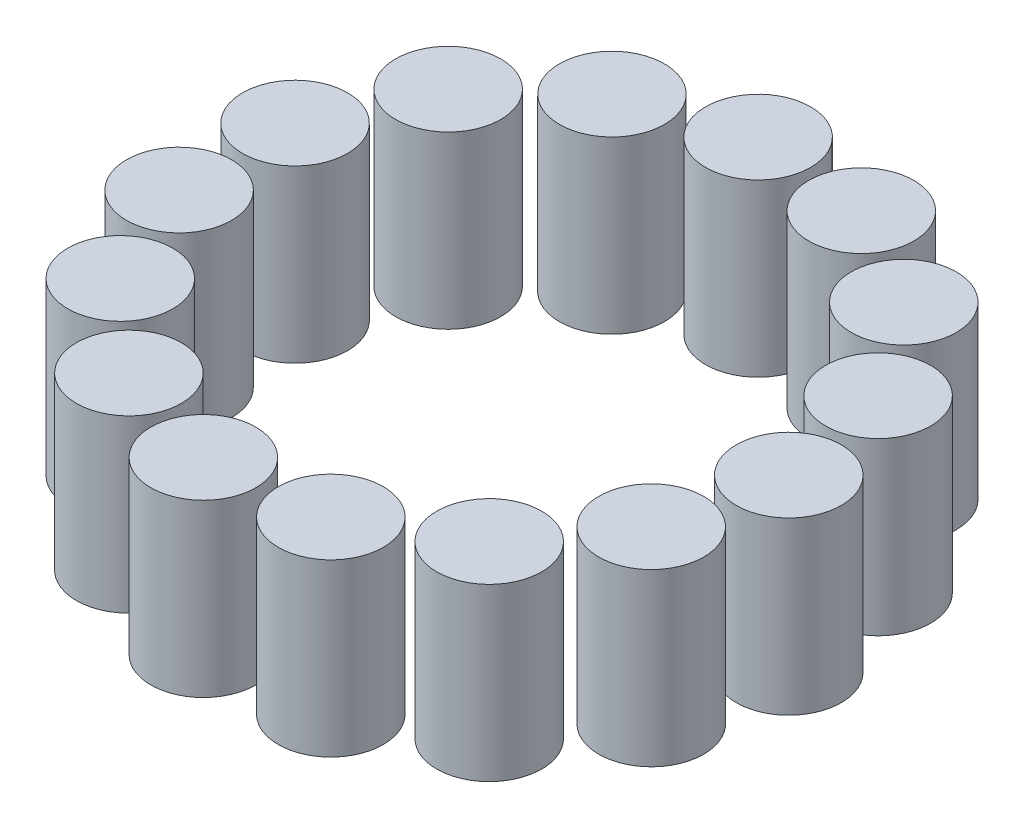
SolidWorks part; units mm, degrees
ref_plane "Front Plane" through (0, 0, 0) normal (0, 0, 1) x (1, 0, 0)
ref_plane "Top Plane" through (0, 0, 0) normal (0, 1, 0) x (1, 0, 0)
ref_plane "Right Plane" through (0, 0, 0) normal (1, 0, 0) x (0, 0, -1)
sketch "Sketch1" plane through (0, 0, 0) normal (0, 1, 0) x (1, 0, 0)
  line L0 (19.4, 0) -> (13.25, 0) construction
  circle A0 centre (0, 0) radius 19.4 construction
  circle A1 centre (0, 0) radius 13.25 construction
  circle A2 centre (16.325, 0) radius 3.075
  dimension "D1" = 38.8
  dimension "D2" = 26.5
extrude "Boss-Extrude1" add sketch "Sketch1" along normal blind 10
sketch "Sketch3" plane through (0, 0, 0) normal (0, 0, 1) x (1, 0, 0)
  line L0 (0, 0) -> (0, 9.984) construction
pattern_circular "CirPattern1" count 15 over 360 about axis through (0, 0, 0) along (0, 1, 0) of "Boss-Extrude1"
